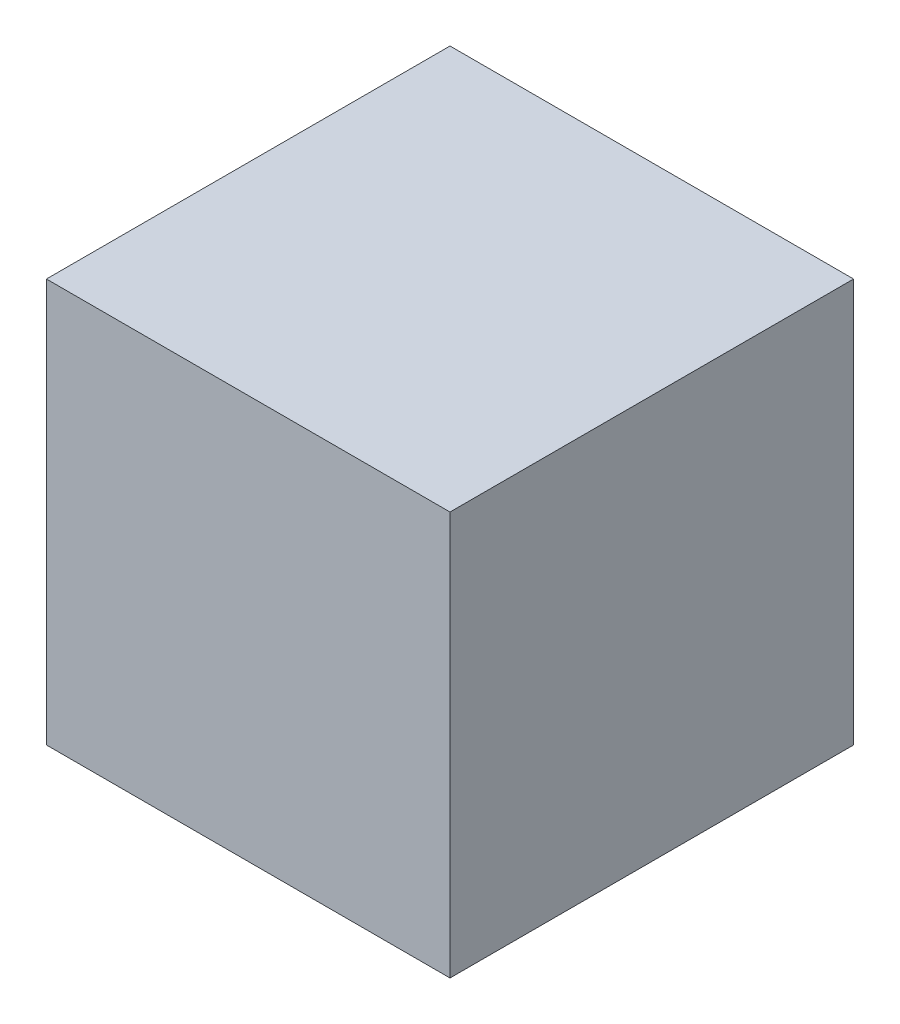
SolidWorks part; units mm, degrees
ref_plane "Спереди" through (0, 0, 0) normal (0, 0, 1) x (1, 0, 0)
ref_plane "Сверху" through (0, 0, 0) normal (0, 1, 0) x (1, 0, 0)
ref_plane "Справа" through (0, 0, 0) normal (1, 0, 0) x (0, 0, -1)
sketch "Эскиз1" plane through (0, 0, 0) normal (0, 0, 1) x (1, 0, 0)
  line L1 (-100, 100) -> (100, 100)
  line L2 (-100, 100) -> (-100, -100)
  line L3 (-100, -100) -> (100, -100)
  line L4 (100, 100) -> (100, -100)
  line L5 (-100, 100) -> (100, -100) construction
  line L6 (-100, -100) -> (100, 100) construction
  point P0 (0, 0)
  dimension "D1" = 200
  dimension "D2" = 200
extrude "Бобышка-Вытянуть1" add sketch "Эскиз1" along normal blind 200 contours L2 L3 L4 L1
